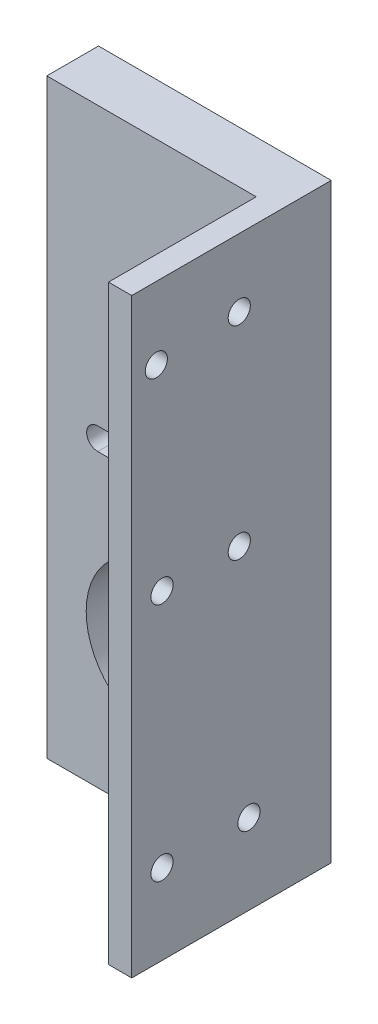
SolidWorks part; units mm, degrees
ref_plane "前视基准面" through (0, 0, 0) normal (0, 0, 1) x (1, 0, 0)
ref_plane "上视基准面" through (0, 0, 0) normal (0, 1, 0) x (1, 0, 0)
ref_plane "右视基准面" through (0, 0, 0) normal (1, 0, 0) x (0, 0, -1)
sketch "草图1" plane through (0, 0, 0) normal (0, 0, 1) x (1, 0, 0)
  line L10 (8.85, 15.7917) -> (-8.85, 15.7917)
  line L11 (8.85, 12.7917) -> (-8.85, 12.7917)
  line L12 (-15.7504, 53.3771) -> (-15.7504, -26.6229)
  line L13 (15.7504, 53.3771) -> (-15.7504, 53.3771)
  line L14 (15.7504, 53.3771) -> (15.7504, -26.6229)
  line L15 (15.7504, -26.6229) -> (-15.7504, -26.6229)
  circle A4 centre (0, -6.7083) radius 10.4175
  arc A5 (-8.85, 15.7917) -> (-8.85, 12.7917) centre (-8.85, 14.2917) ccw
  arc A6 (8.85, 12.7917) -> (8.85, 15.7917) centre (8.85, 14.2917) ccw
  circle A8 centre (0, -20.2083) radius 1.56
  dimension "D1" = 3.12
  dimension "D2" = 80
extrude "凸台-拉伸1" add sketch "草图1" along normal blind 7
sketch "草图3" plane through (0, 0, 0) normal (0, 0, -1) x (-1, 0, 0)
  line L0 (0, 53.3771) -> (0, -24.925)
  line L1 (-15.7504, 53.3771) -> (15.7504, 53.3771) construction
  line L2 (-15.7504, 53.3771) -> (-15.7504, -26.6229) construction
  line L3 (-15.7504, 50.3771) -> (15.7504, 50.3771)
  line L4 (-15.7504, 50.3771) -> (-15.7504, 53.3771)
  line L5 (-15.7504, 53.3771) -> (15.7504, 53.3771)
  line L6 (15.7504, 50.3771) -> (15.7504, 53.3771)
  line L7 (15.7504, 53.3771) -> (15.7504, -26.6229) construction
  dimension "D1" = 3
sketch "草图4" plane through (0, 0, 0) normal (0, 0, -1) x (-1, 0, 0)
  line L0 (-15.7504, 53.3771) -> (-15.7504, -26.6229) construction
  line L1 (-15.7504, -23.5462) -> (15.7504, -23.5462)
  line L2 (-15.7504, -23.5462) -> (-15.7504, -27.6335)
  line L3 (-15.7504, -27.6335) -> (15.7504, -27.6335)
  line L4 (15.7504, -23.5462) -> (15.7504, -27.6335)
sketch "草图5" plane through (0, 0, 0) normal (0, 0, 1) x (1, 0, 0)
  line L0 (15.7504, 53.3771) -> (12.6027, 53.3771)
  line L1 (15.7504, 53.3771) -> (-15.7504, 53.3771) construction
  line L2 (12.6027, 53.3771) -> (12.6027, -26.6229)
  line L3 (15.7504, -26.6229) -> (-15.7504, -26.6229) construction
  line L4 (12.6027, -26.6229) -> (15.7504, -26.6229)
  line L5 (15.7504, -26.6229) -> (15.7504, 53.3771)
extrude "凸台-拉伸2" add sketch "草图5" along normal blind 27
hole_wizard "大小mm 暗销孔1" positions "草图6" profile "草图7" hole size "Ø3.0" standard "ISO" end condition up to next
sketch "草图6" plane through (12.6027, 0, 0) normal (-1, 0, 0) x (0, 0, 1)
  point P0 (12.4448, 44.1925)
  point P2 (23.6738, 43.5785)
  point P4 (11.1301, -15.7392)
  point P6 (22.9001, -15.7392)
  point P8 (12.4448, 16.7045)
  point P10 (22.9001, 16.7045)
sketch "草图7" plane through (12.6027, 44.1925, 12.4448) normal (0, 1, 0) x (0, 0, 1)
  line L0 (0, 0) -> (0, 3.1477)
  line L1 (0, 3.1477) -> (1.5, 3.1477)
  line L2 (1.5, 3.1477) -> (1.5, 0)
  line L5 (1.5, 0) -> (0, 0)
  line L11 (0, -6.35) -> (0, 107.95) construction
  dimension "通孔孔直径" = 3
  dimension "通孔孔深度" = 3.1477
